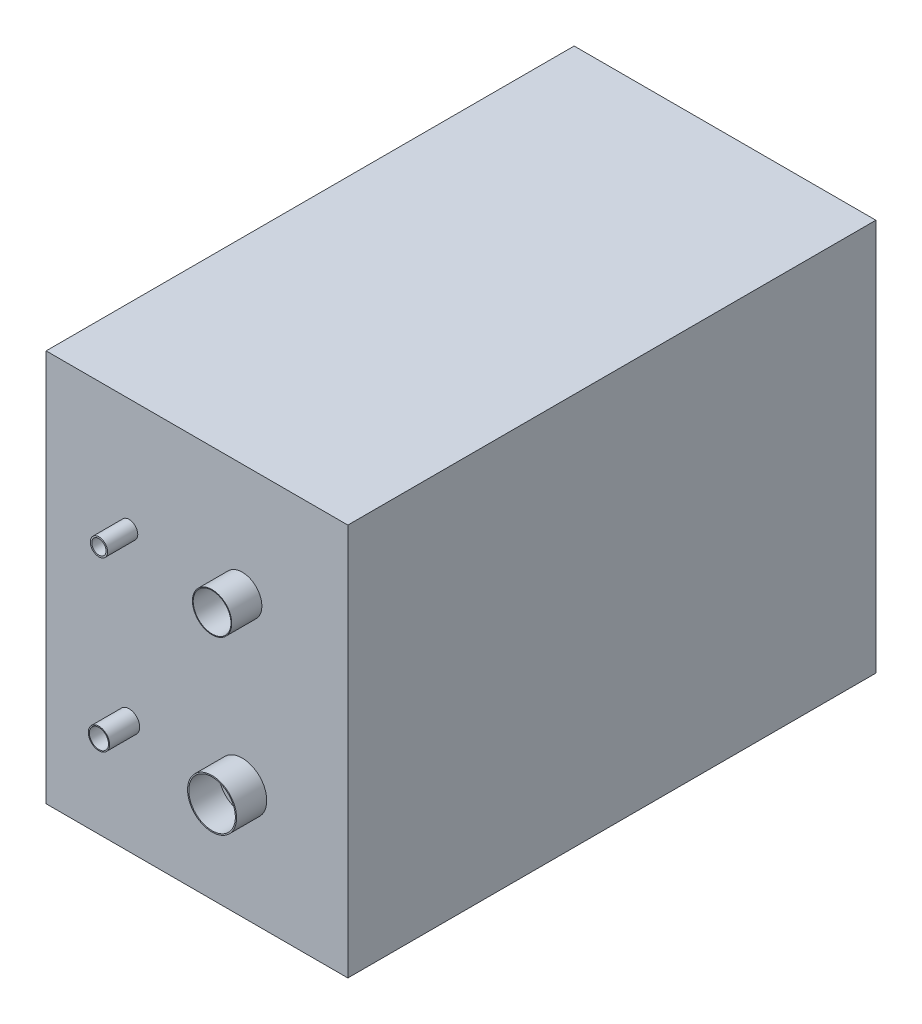
SolidWorks part; units mm, degrees
ref_plane "Front Plane" through (0, 0, 0) normal (0, 0, 1) x (1, 0, 0)
ref_plane "Top Plane" through (0, 0, 0) normal (0, 1, 0) x (1, 0, 0)
ref_plane "Right Plane" through (0, 0, 0) normal (1, 0, 0) x (0, 0, -1)
sketch "Sketch1" plane through (0, 0, 0) normal (0, 0, 1) x (1, 0, 0)
  line L1 (-3900, 5171.5065) -> (-1900, 5171.5065)
  line L2 (-3900, 5171.5065) -> (-3900, 2571.5065)
  line L3 (-3900, 2571.5065) -> (-1900, 2571.5065)
  line L4 (-1900, 5171.5065) -> (-1900, 2571.5065)
  dimension "D1" = 2600
  dimension "D2" = 2000
extrude "Extrude1" add sketch "Sketch1" along normal blind 3500
sketch "Sketch2" plane through (0, 0, 3500) normal (0, 0, 1) x (1, 0, 0)
  line L0 (-1900, 2571.5065) -> (-1900, 5171.5065) construction
  line L1 (-3900, 2571.5065) -> (-1900, 2571.5065) construction
  circle A0 centre (-2600, 3321.5065) radius 162.5
  circle A1 centre (-3350, 3321.5065) radius 70.5
  circle A2 centre (-2600, 4421.5065) radius 130
  circle A3 centre (-3350, 4421.5065) radius 57.5
  circle A4 centre (-2600, 3321.5065) radius 154.5
  circle A5 centre (-3350, 4421.5065) radius 47.5
  circle A6 centre (-2600, 4421.5065) radius 125
  circle A7 centre (-3350, 3321.5065) radius 63.5
  dimension "D13" = 141
  dimension "D14" = 325
  dimension "D15" = 115
  dimension "D16" = 260
  dimension "D1" = 700
  dimension "D2" = 750
  dimension "D3" = 1100
  dimension "D4" = 750
  dimension "D5" = 750
  dimension "D6" = 1100
  dimension "D7" = 700
  dimension "D8" = 750
  dimension "D9" = 8
  dimension "D10" = 10
  dimension "D11" = 5
  dimension "D12" = 7
extrude "Extrude2" add sketch "Sketch2" along normal blind 200
